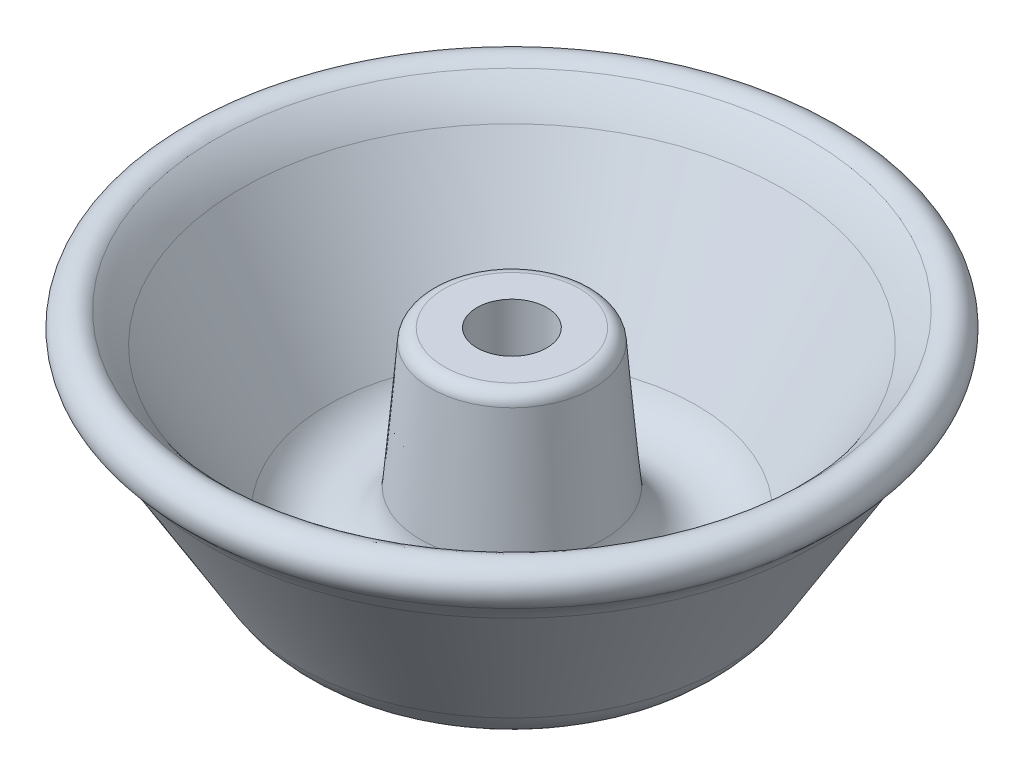
SolidWorks part; units mm, degrees
ref_plane "Front Plane" through (0, 0, 0) normal (0, 0, 1) x (1, 0, 0)
ref_plane "Top Plane" through (0, 0, 0) normal (0, 1, 0) x (1, 0, 0)
ref_plane "Right Plane" through (0, 0, 0) normal (1, 0, 0) x (0, 0, -1)
sketch "Sketch1" plane through (0, 0, 0) normal (0, 0, 1) x (1, 0, 0)
  line L0 (0, 0) -> (0, 30.1625) construction
  line L1 (4.1672, 27.7812) -> (8.0683, 27.7812)
  line L2 (9.65, 26.3299) -> (10.936, 11.3955)
  line L3 (4.1672, 27.7812) -> (4.1672, 11.9062)
  line L4 (0, 0) -> (36.9094, 0) construction
  line L5 (21.9634, 8.8292) -> (32.3203, 25.9824)
  line L6 (36.3972, 23.5207) -> (25.5428, 5.5435)
  line L7 (0, 30.1625) -> (36.9094, 30.1625) construction
  arc A3 (4.1672, 11.9062) -> (4.9819, 7.4307) centre (16.8672, 11.9062) ccw
  arc A4 (10.936, 11.3955) -> (21.9634, 8.8292) centre (16.8672, 11.9062) ccw
  arc A5 (38.4696, 25.9824) -> (35.3491, 29.5801) centre (36.9094, 27.7812) ccw
  arc A6 (32.3203, 25.9824) -> (35.3491, 29.5801) centre (45.2307, 18.1872) cw
  arc A7 (36.3972, 23.5207) -> (38.4696, 25.9824) centre (45.2307, 18.1872) cw
  arc A8 (25.5428, 5.5435) -> (4.9819, 7.4307) centre (15.7201, 11.4743) cw
  arc A9 (8.0683, 27.7812) -> (9.65, 26.3299) centre (8.0683, 26.1938) cw
  point P8 (0, 0)
  point P12 (44.0352, 30.1625)
  point P16 (43.4671, 0)
  point P20 (9.525, 27.7812)
  dimension "D4" = 9.525
  dimension "D3" = 12.7
  dimension "D6" = 5.9531
  dimension "D8" = 4.7625
  dimension "D9" = 39.2906
  dimension "D10" = 15.0812
  dimension "D7" = 10.3187
  dimension "D13" = 1.5875
  dimension "D1" = 30.1625
  dimension "D2" = 4.1672
  dimension "D5" = 27.7812
  dimension "D11" = 15.875
  dimension "D12" = 4.7625
revolve "Revolve1" add sketch "Sketch1" angle 360 about L0
